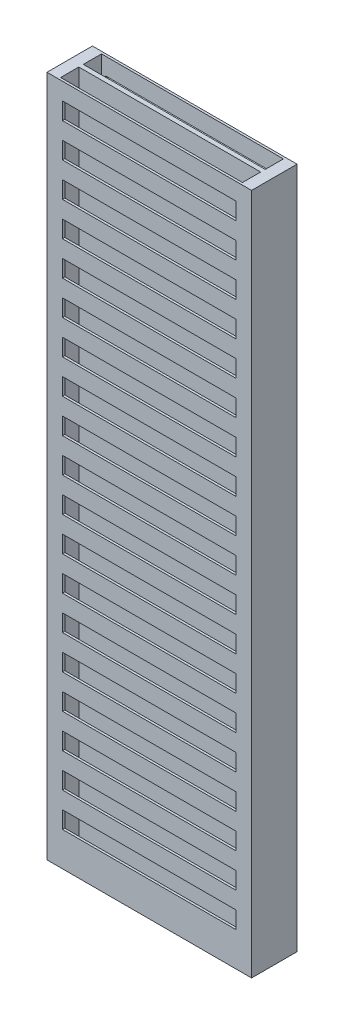
SolidWorks part; units mm, degrees
ref_plane "Front Plane" through (0, 0, 0) normal (0, 0, 1) x (1, 0, 0)
ref_plane "Top Plane" through (0, 0, 0) normal (0, 1, 0) x (1, 0, 0)
ref_plane "Right Plane" through (0, 0, 0) normal (1, 0, 0) x (0, 0, -1)
sketch "Sketch1" plane through (0, 0, 0) normal (0, 1, 0) x (1, 0, 0)
  line L1 (-4.5, -1) -> (4.5, -1)
  line L2 (-4.5, -1) -> (-4.5, 1)
  line L3 (-4.5, 1) -> (4.5, 1)
  line L4 (4.5, -1) -> (4.5, 1)
  line L5 (-4.5, -1) -> (4.5, 1) construction
  line L6 (-4.5, 1) -> (4.5, -1) construction
  point P0 (0, 0)
  dimension "D1" = 9
  dimension "D2" = 2
extrude "Boss-Extrude1" add sketch "Sketch1" along normal mid plane 30
sketch "Sketch2" plane through (0, 15, 0) normal (0, 1, 0) x (1, 0, 0)
  line L1 (-4, 0.1) -> (4, 0.1)
  line L2 (-4, 0.1) -> (-4, 0.9)
  line L3 (-4, 0.9) -> (4, 0.9)
  line L4 (4, 0.1) -> (4, 0.9)
  line L5 (-4, 0.1) -> (4, 0.9) construction
  line L6 (-4, 0.9) -> (4, 0.1) construction
  point P0 (0, 0.5)
  dimension "D1" = 0.8
  dimension "D2" = 8
  dimension "D3" = 0
  dimension "D4" = 0.5
extrude "Cut-Extrude1" cut sketch "Sketch2" against normal through all and the other way through all
mirror "Mirror1" about plane through (0, 0, 0) normal (0, 0, 1) of "Cut-Extrude1"
sketch "Sketch3" plane through (0, 0, 1) normal (0, 0, 1) x (1, 0, 0)
  line L0 (0, -1.1) -> (0, 1.1) construction
  line L1 (-3.8171, 13.5) -> (3.8171, 13.5)
  line L2 (-3.8171, 13.5) -> (-3.8171, 14.25)
  line L3 (-3.8171, 14.25) -> (3.8171, 14.25)
  line L4 (3.8171, 13.5) -> (3.8171, 14.25)
  line L5 (-3.8171, 13.5) -> (3.8171, 14.25) construction
  line L6 (-3.8171, 14.25) -> (3.8171, 13.5) construction
  line L7 (-4.5, 15) -> (4.5, 15) construction
  point P0 (0, 13.875)
  dimension "D1" = 0.75
  dimension "D2" = 0.75
extrude "Cut-Extrude2" cut sketch "Sketch3" against normal up to next (0.1 mm away)
pattern_linear "LPattern1" count 19 spacing 1.5 along (0, -1, 0) of "Cut-Extrude2"
mirror "Mirror2" about plane through (0, 0, 0) normal (0, 0, 1) of "LPattern1", "Cut-Extrude2"
